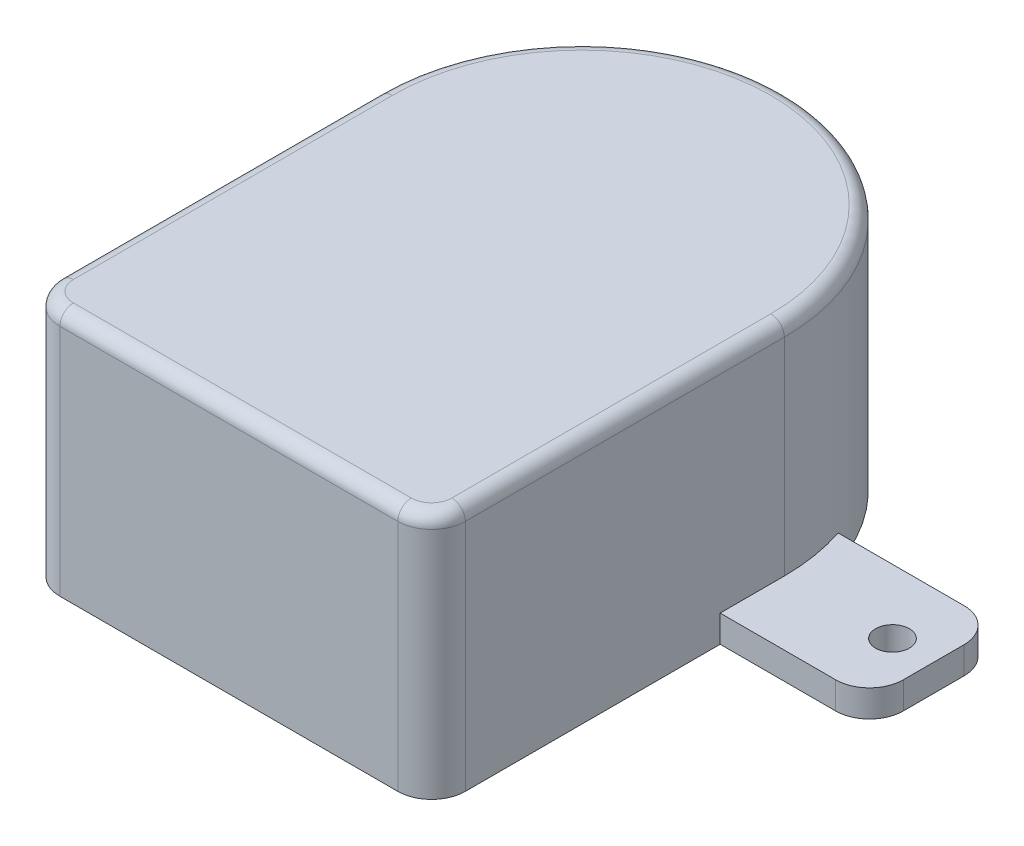
SolidWorks part; units mm, degrees
material "PUR"
ref_plane "Front Plane" through (0, 0, 0) normal (0, 0, 1) x (1, 0, 0)
ref_plane "Top Plane" through (0, 0, 0) normal (0, 1, 0) x (1, 0, 0)
ref_plane "Right Plane" through (0, 0, 0) normal (1, 0, 0) x (0, 0, -1)
sketch "Sketch1" plane through (0, 0, 0) normal (0, 1, 0) x (1, 0, 0)
  line L0 (-15, 0) -> (-15, -26.1)
  line L1 (-15, -26.1) -> (15, -26.1)
  line L2 (15, -26.1) -> (15, 0)
  arc A0 (15, 0) -> (-15, 0) centre (0, 0) ccw
  point P1 (0, 15)
  point P6 (0, -26.1)
  dimension "D1" = 30
  dimension "D2" = 41.1
extrude "Boss-Extrude1" add sketch "Sketch1" along normal blind 18.3
sketch "Sketch2" plane through (0, 0, 0) normal (0, 1, 0) x (1, 0, 0)
  line L0 (-23, 0) -> (23, 0) construction
  line L2 (23.55, -4.75) -> (-23.55, -4.75)
  line L3 (26.05, -2.25) -> (26.05, 2.25)
  line L4 (23.55, 4.75) -> (-23.55, 4.75)
  line L5 (-26.05, -2.25) -> (-26.05, 2.25)
  line L6 (26.05, -4.75) -> (-26.05, 4.75) construction
  line L7 (26.05, 4.75) -> (-26.05, -4.75) construction
  arc A0 (26.05, 2.25) -> (23.55, 4.75) centre (23.55, 2.25) ccw
  arc A1 (23.55, -4.75) -> (26.05, -2.25) centre (23.55, -2.25) ccw
  arc A2 (-23.55, -4.75) -> (-26.05, -2.25) centre (-23.55, -2.25) cw
  arc A3 (-23.55, 4.75) -> (-26.05, 2.25) centre (-23.55, 2.25) ccw
  circle A4 centre (-23, 0) radius 1.25
  circle A5 centre (23, 0) radius 1.25
  point P3 (0, 0)
  point P4 (0, 0)
  dimension "D4" = 2.5
  dimension "D5" = 2.5
  dimension "D1" = 52.1
  dimension "D2" = 9.5
  dimension "D3" = 46
extrude "Boss-Extrude2" add sketch "Sketch2" along normal blind 2
fillet "Fillet1" radius 2.5 2 edges at (-15, 9.15, 26.1) (15, 9.15, 26.1)
sketch "Sketch3" plane through (0, 0, 0) normal (0, -1, 0) x (-1, 0, 0)
  line L0 (12.5, -26.1) -> (-12.5, -26.1) construction
  circle A0 centre (0, 0.1) radius 5.5
  dimension "D2" = 11
  dimension "D1" = 26.2
extrude "Cut-Extrude2" cut sketch "Sketch3" against normal blind 5
sketch "Sketch5" plane through (0, 0, 0) normal (0, -1, 0) x (-1, 0, 0)
  circle A0 centre (0, 0.1) radius 4
  dimension "D1" = 8
extrude "Cut-Extrude3" cut sketch "Sketch5" against normal blind 15
fillet "Fillet2" radius 1 6 edges at (14.2678, 18.3, 25.3678) (0, 18.3, 26.1) (-14.2678, 18.3, 25.3678) (-15, 18.3, 11.8) (0, 18.3, -15) (15, 18.3, 11.8)
